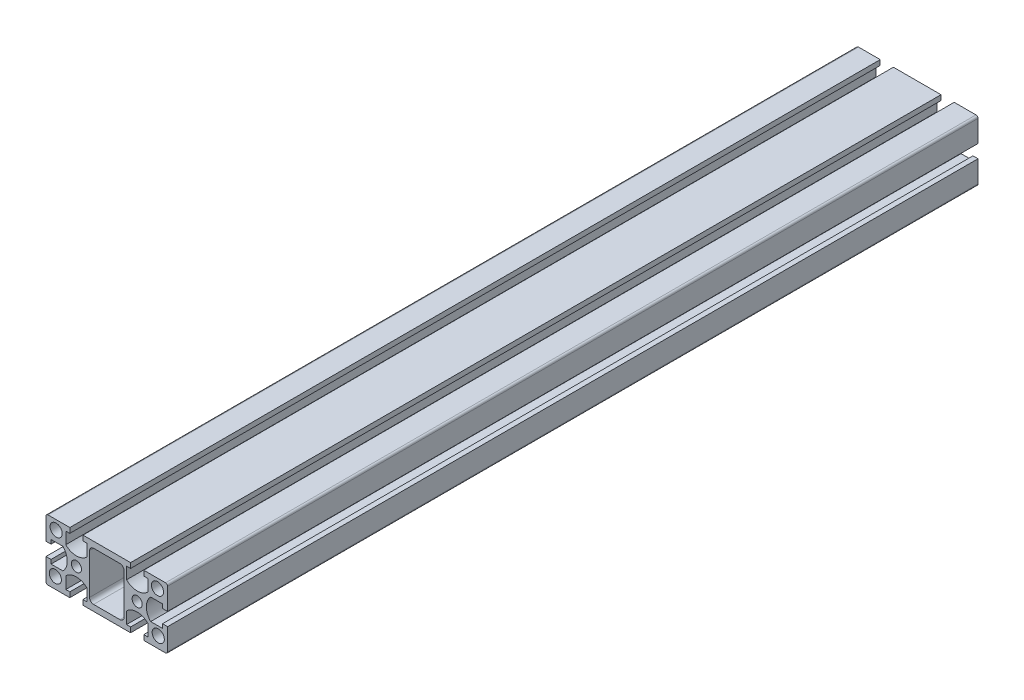
SolidWorks part; units mm, degrees
ref_plane "Front Plane" through (0, 0, 0) normal (0, 0, 1) x (1, 0, 0)
ref_plane "Top Plane" through (0, 0, 0) normal (0, 1, 0) x (1, 0, 0)
ref_plane "Right Plane" through (0, 0, 0) normal (1, 0, 0) x (0, 0, -1)
sketch "Model" plane through (0, 0, 0) normal (0, 0, 1) x (1, 0, 0)
  line L0 (6.5, 12) -> (-6.5, 12)
  line L1 (8.5, 10) -> (8.5, -10)
  line L2 (6.5, -12) -> (-6.5, -12)
  line L3 (-8.5, 10) -> (-8.5, -10)
  line L4 (-27.5, 3.25) -> (-30, 3.25)
  line L5 (-30, -3.25) -> (-27.5, -3.25)
  line L6 (-21.6439, 5.25) -> (-27.5, 5.25)
  line L7 (-27.5, 5.25) -> (-27.5, 3.25)
  line L8 (-21.6439, -5.25) -> (-27.5, -5.25)
  line L9 (-27.5, -5.25) -> (-27.5, -3.25)
  line L10 (-18.25, 15) -> (-18.25, 12.5)
  line L11 (-20.25, 12.5) -> (-18.25, 12.5)
  line L12 (-20.25, 6.6439) -> (-20.25, 12.5)
  line L13 (-9.75, 6.6439) -> (-9.75, 12.5)
  line L14 (-9.75, 12.5) -> (-11.75, 12.5)
  line L15 (-11.75, 12.5) -> (-11.75, 15)
  line L16 (-11.75, -15) -> (-11.75, -12.5)
  line L17 (-9.75, -12.5) -> (-11.75, -12.5)
  line L18 (-9.75, -6.6439) -> (-9.75, -12.5)
  line L19 (-20.25, -6.6439) -> (-20.25, -12.5)
  line L20 (-20.25, -12.5) -> (-18.25, -12.5)
  line L21 (-18.25, -12.5) -> (-18.25, -15)
  line L22 (18.25, -12.5) -> (18.25, -15)
  line L23 (20.25, -12.5) -> (18.25, -12.5)
  line L24 (20.25, -6.6439) -> (20.25, -12.5)
  line L25 (9.75, -6.6439) -> (9.75, -12.5)
  line L26 (9.75, -12.5) -> (11.75, -12.5)
  line L27 (11.75, -15) -> (11.75, -12.5)
  line L28 (27.5, 3.25) -> (30, 3.25)
  line L29 (27.5, 5.25) -> (27.5, 3.25)
  line L30 (21.6439, 5.25) -> (27.5, 5.25)
  line L31 (21.6439, -5.25) -> (27.5, -5.25)
  line L32 (27.5, -5.25) -> (27.5, -3.25)
  line L33 (30, -3.25) -> (27.5, -3.25)
  line L34 (11.75, 12.5) -> (11.75, 15)
  line L35 (9.75, 12.5) -> (11.75, 12.5)
  line L36 (9.75, 6.6439) -> (9.75, 12.5)
  line L37 (20.25, 6.6439) -> (20.25, 12.5)
  line L38 (20.25, 12.5) -> (18.25, 12.5)
  line L39 (18.25, 15) -> (18.25, 12.5)
  line L40 (-18.25, 15) -> (-29, 15)
  line L41 (-30, 14) -> (-30, 3.25)
  line L42 (-30, -3.25) -> (-30, -14)
  line L43 (-29, -15) -> (-18.25, -15)
  line L44 (-11.75, -15) -> (11.75, -15)
  line L45 (18.25, -15) -> (29, -15)
  line L46 (30, -14) -> (30, -3.25)
  line L47 (30, 3.25) -> (30, 14)
  line L48 (29, 15) -> (18.25, 15)
  line L49 (11.75, 15) -> (-11.75, 15)
  circle A0 centre (-15, 0) radius 2.5
  circle A1 centre (-25, 10.5314) radius 3
  circle A2 centre (-25.3993, -9.4686) radius 3
  arc A3 (-21.6439, -5.25) -> (-21.6439, 5.25) centre (-27, 0) ccw
  arc A4 (-20.25, 6.6439) -> (-9.75, 6.6439) centre (-15, 12) ccw
  arc A5 (-9.75, -6.6439) -> (-20.25, -6.6439) centre (-15, -12) ccw
  circle A6 centre (25.3993, -9.4686) radius 3
  arc A7 (20.25, -6.6439) -> (9.75, -6.6439) centre (15, -12) ccw
  circle A8 centre (15, 0) radius 2.5
  arc A9 (21.6439, 5.25) -> (21.6439, -5.25) centre (27, 0) ccw
  circle A10 centre (25, 10.5314) radius 3
  arc A11 (9.75, 6.6439) -> (20.25, 6.6439) centre (15, 12) ccw
  arc A12 (30, 14) -> (29, 15) centre (29, 14) ccw
  arc A13 (29, -15) -> (30, -14) centre (29, -14) ccw
  arc A14 (-30, -14) -> (-29, -15) centre (-29, -14) ccw
  arc A15 (-29, 15) -> (-30, 14) centre (-29, 14) ccw
  arc A16 (-8.5, -10) -> (-6.5, -12) centre (-6.5, -10) ccw
  arc A17 (6.5, -12) -> (8.5, -10) centre (6.5, -10) ccw
  arc A18 (8.5, 10) -> (6.5, 12) centre (6.5, 10) ccw
  arc A19 (-6.5, 12) -> (-8.5, 10) centre (-6.5, 10) ccw
  point P90 (0, 0)
  point P91 (0, 0)
extrude "Boss-Extrude1" add sketch "Model" along normal blind 400
